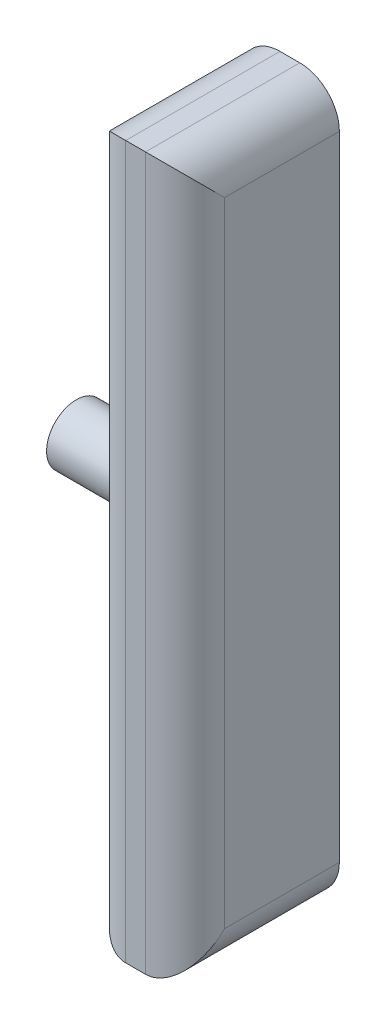
SolidWorks part; units mm, degrees
ref_plane "Front Plane" through (0, 0, 0) normal (0, 0, 1) x (1, 0, 0)
ref_plane "Top Plane" through (0, 0, 0) normal (0, 1, 0) x (1, 0, 0)
ref_plane "Right Plane" through (0, 0, 0) normal (1, 0, 0) x (0, 0, -1)
sketch "Sketch1" plane through (0, 0, 0) normal (1, 0, 0) x (0, 0, -1)
  circle A0 centre (0, 0) radius 7.5
  dimension "D1" = 15
extrude "Boss-Extrude1" add sketch "Sketch1" along normal blind 22
sketch "Sketch2" plane through (22, 0, 0) normal (1, 0, 0) x (0, 0, -1)
  line L0 (-19.5, 0) -> (19.5, 0) construction
  line L1 (-19.5, 90) -> (19.5, 90)
  line L2 (-19.5, 90) -> (-19.5, -90)
  line L3 (-19.5, -90) -> (19.5, -90)
  line L4 (19.5, 90) -> (19.5, -90)
  dimension "D1" = 180
  dimension "D2" = 39
extrude "Boss-Extrude2" add sketch "Sketch2" along normal blind 25
fillet "Fillet1" radius 10 6 edges at (22, 90, 0) (47, 90, 0) (22, -90, 0) (47, -90, 0) (47, 0, 19.5) (22, 0, 19.5)
